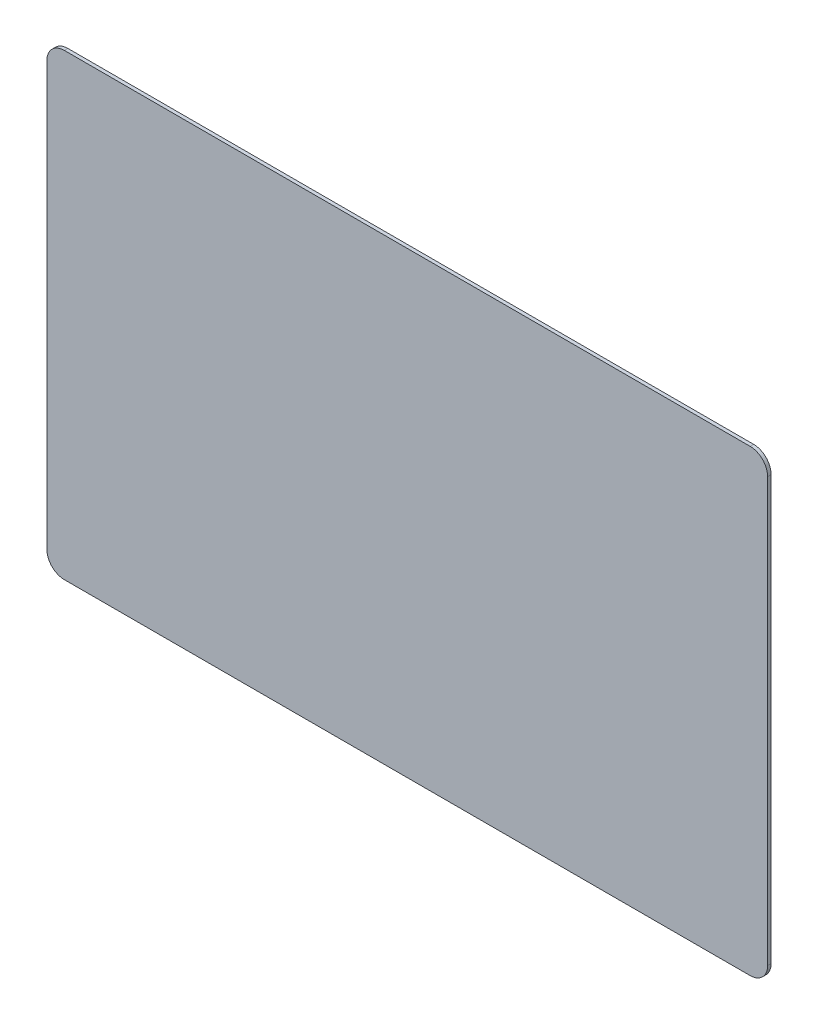
SolidWorks part; units mm, degrees
ref_plane "Ön Düzlem" through (0, 0, 0) normal (0, 0, 1) x (1, 0, 0)
ref_plane "Üst Düzlem" through (0, 0, 0) normal (0, 1, 0) x (1, 0, 0)
ref_plane "Sağ Düzlem" through (0, 0, 0) normal (1, 0, 0) x (0, 0, -1)
sketch "Çizim1" plane through (0, 0, 0) normal (0, 0, 1) x (1, 0, 0)
  line L1 (-124.5029, 127.4585) -> (267.4971, 127.4585)
  line L2 (-134.5029, 117.4585) -> (-134.5029, -124.5415)
  line L3 (-124.5029, -134.5415) -> (267.4971, -134.5415)
  line L4 (277.4971, 117.4585) -> (277.4971, -124.5415)
  arc A0 (-124.5029, -134.5415) -> (-134.5029, -124.5415) centre (-124.5029, -124.5415) cw
  arc A1 (-134.5029, 117.4585) -> (-124.5029, 127.4585) centre (-124.5029, 117.4585) cw
  arc A2 (277.4971, 117.4585) -> (267.4971, 127.4585) centre (267.4971, 117.4585) ccw
  arc A3 (267.4971, -134.5415) -> (277.4971, -124.5415) centre (267.4971, -124.5415) ccw
  point P10 (-134.5029, 127.4585)
  point P15 (277.4971, -134.5415)
  dimension "D1" = 10
extrude "Yükseklik-Ekstrüzyon1" add sketch "Çizim1" along normal blind 2 contours L3 A3 L4 A2 L1 A1 L2 A0
